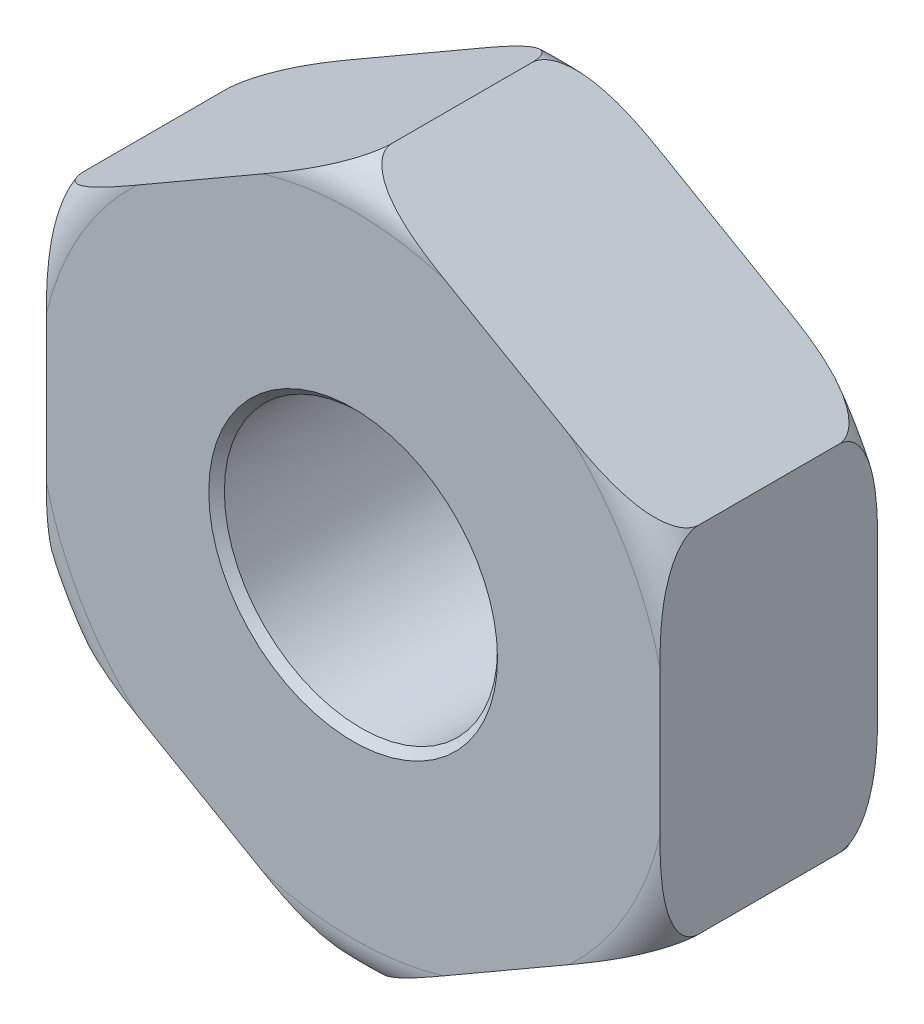
SolidWorks part; units mm, degrees
ref_plane "Front" through (0, 0, 0) normal (0, 0, 1) x (1, 0, 0)
ref_plane "Top" through (0, 0, 0) normal (0, 1, 0) x (1, 0, 0)
ref_plane "Right" through (0, 0, 0) normal (1, 0, 0) x (0, 0, -1)
sketch "Sketch1" plane through (0, 0, 0) normal (0, 0, 1) x (1, 0, 0)
  line L1 (0, 4.5461) -> (-3.937, 2.273)
  line L2 (-3.937, 2.273) -> (-3.937, -2.273)
  line L3 (-3.937, -2.273) -> (0, -4.5461)
  line L4 (0, -4.5461) -> (3.937, -2.273)
  line L5 (3.937, -2.273) -> (3.937, 2.273)
  line L6 (3.937, 2.273) -> (0, 4.5461)
  circle A0 centre (0, 0) radius 3.937 construction
  circle A1 centre (0, 0) radius 1.7525
  dimension "D" = 3.505
  dimension "A" = 7.874
extrude "Base-Extrude" add sketch "Sketch1" along normal mid plane 2.794
sketch "Sketch2" plane through (0, 0, 0) normal (1, 0, 0) x (0, 0, -1)
  line L0 (0, 0) -> (0, 8.5055) construction
  line L1 (0, 0) -> (6.1188, 0) construction
  line L2 (-1.397, 0) -> (1.397, 0) construction
  line L3 (-1.397, 1.7525) -> (-1.397, 1.8525)
  line L4 (-1.397, -2.273) -> (-1.397, 2.273) construction
  line L5 (-1.397, 1.8525) -> (-1.297, 1.7525)
  line L6 (1.397, 1.7525) -> (-1.397, 1.7525) construction
  line L7 (-1.297, 1.7525) -> (-1.397, 1.7525)
  line L8 (-1.397, 4.5461) -> (-1.397, 4.0461)
  line L9 (-1.397, 2.273) -> (-1.397, 4.5461) construction
  line L10 (-1.397, 4.5461) -> (-0.897, 4.5461)
  line L11 (-1.397, 4.5461) -> (1.397, 4.5461) construction
  line L12 (1.397, 4.5461) -> (0.897, 4.5461)
  line L13 (1.397, 4.5461) -> (1.397, 4.0461)
  line L14 (1.297, 1.7525) -> (1.397, 1.7525)
  line L15 (1.397, 1.8525) -> (1.297, 1.7525)
  line L16 (1.397, 1.7525) -> (1.397, 1.8525)
  arc A0 (-0.897, 4.5461) -> (-1.397, 4.0461) centre (-0.897, 4.0461) ccw
  arc A1 (0.897, 4.5461) -> (1.397, 4.0461) centre (0.897, 4.0461) cw
  dimension "D2" = 0.5
  dimension "D1" = 0.1
revolve "DetailCut" cut sketch "Sketch2" angle 360 about L1
